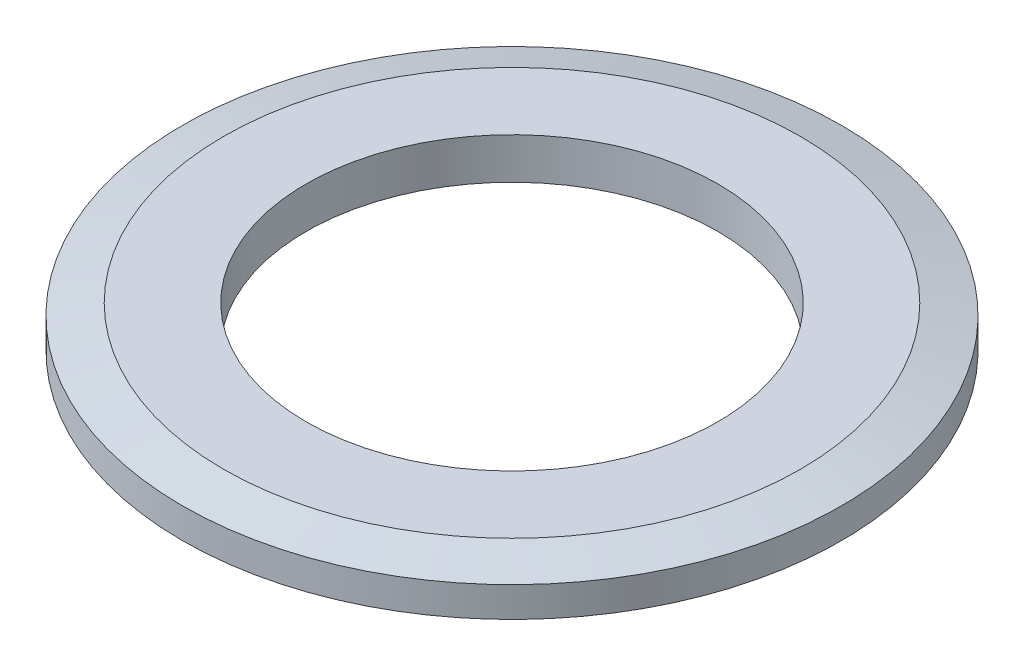
SolidWorks part; units mm, degrees
material "1060 Alloy"
ref_plane "Front Plane" through (0, 0, 0) normal (0, 0, 1) x (1, 0, 0)
ref_plane "Top Plane" through (0, 0, 0) normal (0, 1, 0) x (1, 0, 0)
ref_plane "Right Plane" through (0, 0, 0) normal (1, 0, 0) x (0, 0, -1)
sketch "Sketch1" plane through (0, 0, 0) normal (0, 1, 0) x (1, 0, 0)
  circle A0 centre (0, 0) radius 5
  circle A1 centre (0, 0) radius 8
  dimension "D1" = 10
  dimension "D2" = 16
extrude "Boss-Extrude1" add sketch "Sketch1" along normal blind 1
chamfer "Chamfer1" distance 1 angle 15 1 edges at (0, 1, 8)
